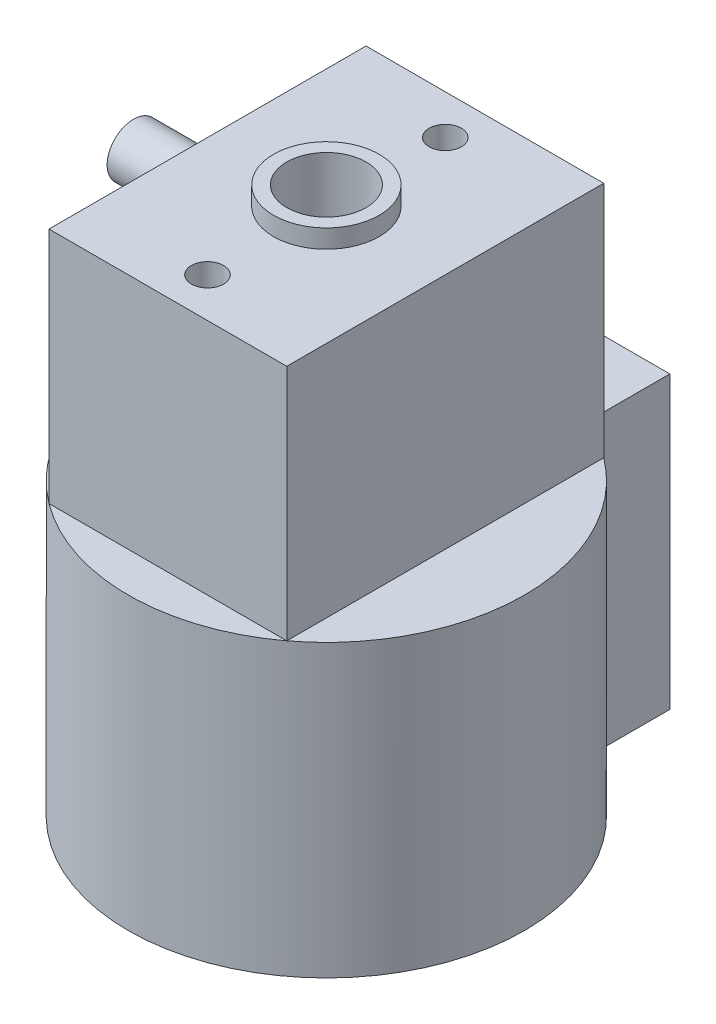
SolidWorks part; units mm, degrees
ref_plane "Front Plane" through (0, 0, 0) normal (0, 0, 1) x (1, 0, 0)
ref_plane "Top Plane" through (0, 0, 0) normal (0, 1, 0) x (1, 0, 0)
ref_plane "Right Plane" through (0, 0, 0) normal (1, 0, 0) x (0, 0, -1)
ref_plane "Plane1"
sketch "Sketch1" plane through (0, 0, 0) normal (0, 1, 0) x (-1, 0, 0)
  line L0 (-3, -7.5) -> (7, -7.5)
  line L1 (7, -7.5) -> (7, -10)
  line L2 (7, -10) -> (-3, -10)
  line L3 (-3, -10) -> (-3, -7.5)
  circle A0 centre (0, 0) radius 7.5
  circle A1 centre (0, 0) radius 1.5
  dimension "D1" = 15
  dimension "D5" = 3
  dimension "D2" = 3
  dimension "D3" = 10
  dimension "D4" = 10
extrude "Extrusion3" add sketch "Sketch1" along normal blind 20 contours L3 L2 L1 L0 | A0 A1
ref_plane "Plane2"
sketch "Sketch2" plane through (0, 20, 0) normal (0, 1, 0) x (1, 0, 0)
  line L0 (15, -15) -> (-15, -15)
  line L1 (-15, -15) -> (-15, 15)
  line L2 (-15, 15) -> (15, 15)
  line L3 (15, 15) -> (15, -15)
  line L4 (4.5, -6) -> (-4.5, -6)
  line L5 (-4.5, -6) -> (-4.5, 6)
  line L6 (-4.5, 6) -> (4.5, 6)
  line L7 (4.5, 6) -> (4.5, -6)
  dimension "D1" = 9
  dimension "D2" = 12
  dimension "D3" = 30
  dimension "D4" = 30
extrude "Extrusion4" cut sketch "Sketch2" against normal blind 9 contours L3 L2 L1 L0 L6 L7 L4 L5
sketch "Sketch3" plane through (-7, 0, 0) normal (-1, 0, 0) x (0, 0, 1)
  circle A0 centre (-8.7, 9.5) radius 1
  circle A1 centre (-8.7, 7) radius 1
  circle A2 centre (-8.7, 4.5) radius 1
  circle A3 centre (-8.7, 2) radius 1
  dimension "D1" = 2
  dimension "D2" = 2.5
  dimension "D3" = 2.5
  dimension "D4" = 2.5
extrude "Extrusion5" add sketch "Sketch3" along normal blind 9
hole_wizard "Hole1" positions "Sketch5" profile "Sketch4" legacy
sketch "Sketch5" plane through (0, 20, 0) normal (0, 1, 0) x (1, 0, 0)
  point P1 (0, -4.5)
  point P2 (0, 4.5)
sketch "Sketch4" plane through (0, 20, 4.5) normal (1, 0, 0) x (0, 0, 1)
  line L0 (0, 0) -> (0, 5.6668)
  line L1 (0, 5.6668) -> (0.6105, 5.3)
  line L2 (0.6105, 5.3) -> (0.6105, 0)
  line L4 (0.6105, 0) -> (0, 0)
  line L6 (0, 5.6668) -> (-0.6105, 5.3) construction
  line L7 (0, -4.2442) -> (0, 117.3081) construction
  dimension "Diameter" = 1.221
  dimension "Depth" = 5.3
  dimension "Drill Angle" = 118
cosmetic thread "Cosmetic Thread1" parameters "D1"=5.3, "D2"=1.736
cosmetic thread "Cosmetic Thread2" parameters "D1"=5.3, "D2"=1.736
ref_plane "Plane3"
sketch "Sketch6" plane through (0, 0, 0) normal (0, -1, 0) x (1, 0, 0)
  circle A0 centre (0, 0) radius 3
  circle A1 centre (0, 0) radius 1.5
  dimension "D1" = 6
extrude "Extrusion6" add sketch "Sketch6" along normal blind 1 contours A0 A1
ref_plane "Plane4"
sketch "Sketch7" plane through (0, 20, 0) normal (0, 1, 0) x (1, 0, 0)
  circle A0 centre (0, 0) radius 2
  circle A1 centre (0, 0) radius 1.5
  dimension "D1" = 4
extrude "Extrusion7" add sketch "Sketch7" along normal blind 0.7 contours A0 A1
